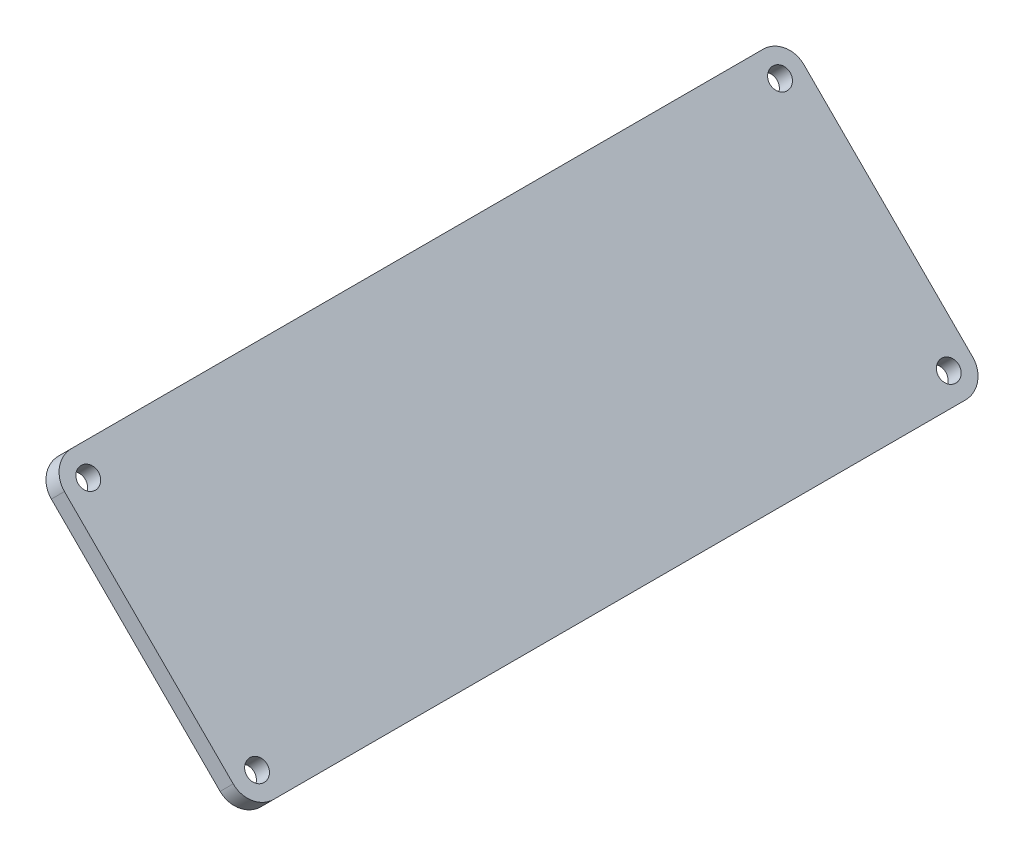
SolidWorks part; units mm, degrees
ref_plane "Front Plane" through (0, 0, 0) normal (0, 0, 1) x (1, 0, 0)
ref_plane "Top Plane" through (0, 0, 0) normal (0, 1, 0) x (1, 0, 0)
ref_plane "Right Plane" through (0, 0, 0) normal (1, 0, 0) x (0, 0, -1)
sketch "Sketch1" plane through (421.8983, 421.8983, 0) normal (0.7071, 0.7071, 0) x (0, 0, -1)
  line L4 (-449.2694, 39.5494) -> (-449.2694, 79.5694)
  line L5 (-569.2694, 35.5494) -> (-453.2694, 35.5494)
  line L6 (-573.2694, 79.5694) -> (-573.2694, 39.5494)
  line L7 (-453.2694, 83.5694) -> (-569.2694, 83.5694)
  circle A0 centre (-569.2694, 79.5694) radius 1.7 construction
  circle A1 centre (-569.2694, 39.5494) radius 1.7 construction
  circle A2 centre (-453.2694, 39.5494) radius 1.7 construction
  circle A3 centre (-453.2694, 79.5694) radius 1.7 construction
  circle A8 centre (-569.2694, 79.5694) radius 1.7
  circle A9 centre (-569.2694, 39.5494) radius 1.7
  circle A10 centre (-453.2694, 39.5494) radius 1.7
  circle A11 centre (-453.2694, 79.5694) radius 1.7
  arc A12 (-449.2694, 79.5694) -> (-453.2694, 83.5694) centre (-453.2694, 79.5694) ccw
  arc A13 (-453.2694, 35.5494) -> (-449.2694, 39.5494) centre (-453.2694, 39.5494) ccw
  arc A14 (-573.2694, 39.5494) -> (-569.2694, 35.5494) centre (-569.2694, 39.5494) ccw
  arc A15 (-569.2694, 83.5694) -> (-573.2694, 79.5694) centre (-569.2694, 79.5694) ccw
  point P22 (0, 0)
  point P23 (0, 0)
  point P26 (0, 0)
  point P27 (0, 0)
  dimension "D1" = 4
extrude "Boss-Extrude1" add sketch "Sketch1" along normal blind 3.1
